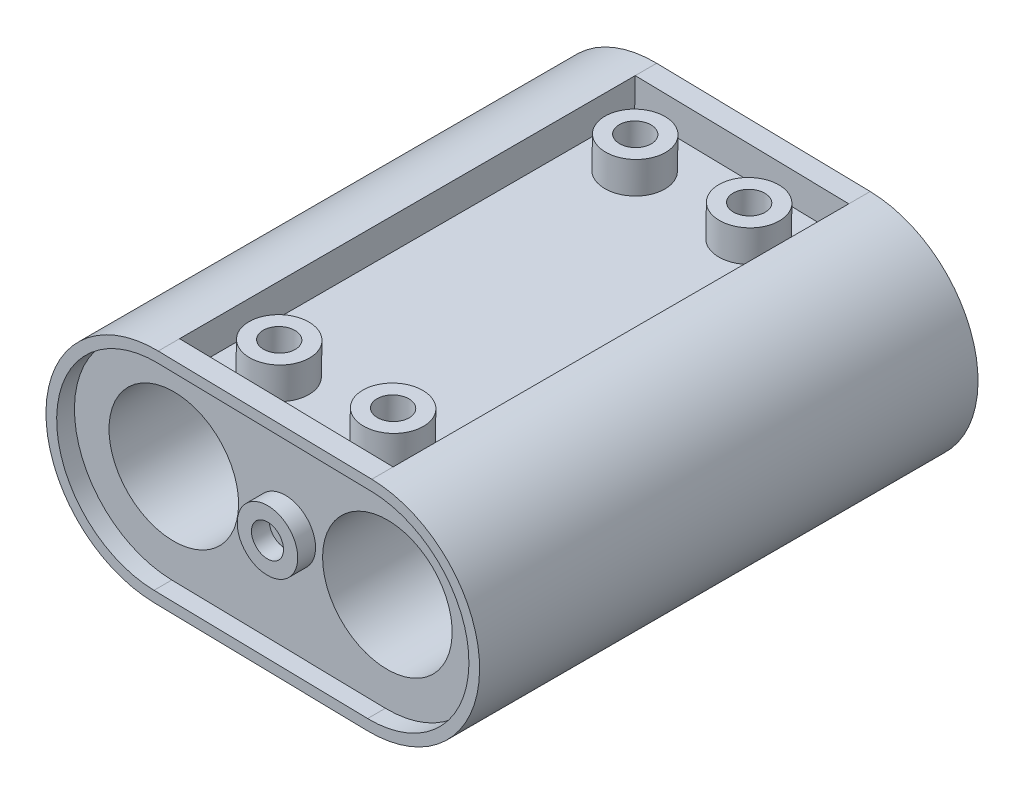
SolidWorks part; units mm, degrees
ref_plane "Спереди" through (0, 0, 0) normal (0, 0, 1) x (1, 0, 0)
ref_plane "Сверху" through (0, 0, 0) normal (0, 1, 0) x (1, 0, 0)
ref_plane "Справа" through (0, 0, 0) normal (1, 0, 0) x (0, 0, -1)
sketch "Эскиз1" plane through (0, 0, 0) normal (0, 0, 1) x (1, 0, 0)
  line L0 (0, 32.6386) -> (-1.3723, -35.9944) construction
  line L1 (-15.6574, -0.089) -> (14.3366, -0.6887) construction
  line L2 (-15.3485, 15.3597) -> (14.6455, 14.76)
  line L3 (-15.9662, -15.5377) -> (14.0278, -16.1374)
  circle A0 centre (-15.6574, -0.089) radius 9.1
  circle A1 centre (14.3366, -0.6887) radius 9.1
  arc A2 (-15.3485, 15.3597) -> (-15.9662, -15.5377) centre (-15.6574, -0.089) ccw
  arc A3 (14.0278, -16.1374) -> (14.6455, 14.76) centre (14.3366, -0.6887) ccw
  point P6 (-0.6604, -0.3889)
  dimension "D1" = 18.2
  dimension "D2" = 15
extrude "Бобышка-Вытянуть1" add sketch "Эскиз1" along normal blind 65
sketch "Эскиз2" plane through (0, 0, 65) normal (0, 0, 1) x (1, 0, 0)
  line L0 (-15.6574, -0.089) -> (14.3366, -0.6887) construction
  line L1 (-15.3785, 13.86) -> (14.6155, 13.2603)
  line L2 (-15.9363, -14.038) -> (14.0577, -14.6377)
  line L3 (14.6455, 14.76) -> (-15.3485, 15.3597) construction
  line L4 (-15.9662, -15.5377) -> (14.0278, -16.1374) construction
  line L5 (-15.9662, -15.5377) -> (14.0278, -16.1374)
  line L6 (14.6455, 14.76) -> (-15.3485, 15.3597)
  arc A0 (-15.3785, 13.86) -> (-15.9363, -14.038) centre (-15.6574, -0.089) ccw
  arc A1 (14.0577, -14.6377) -> (14.6155, 13.2603) centre (14.3366, -0.6887) ccw
  arc A2 (14.0278, -16.1374) -> (14.6455, 14.76) centre (14.3366, -0.6887) ccw construction
  arc A3 (-15.3485, 15.3597) -> (-15.9662, -15.5377) centre (-15.6574, -0.089) ccw construction
  arc A4 (14.0278, -16.1374) -> (14.6455, 14.76) centre (14.3366, -0.6887) ccw
  arc A5 (-15.3485, 15.3597) -> (-15.9662, -15.5377) centre (-15.6574, -0.089) ccw
  point P4 (-0.6604, -0.3889)
  dimension "D1" = 1.5
extrude "Бобышка-Вытянуть2" add sketch "Эскиз2" along normal blind 2.5
sketch "Эскиз3" plane through (0, 0, 65) normal (0, 0, 1) x (1, 0, 0)
  circle A0 centre (0, 0) radius 2.25
  circle A1 centre (0, 0) radius 4.25
  dimension "D1" = 4.5
  dimension "D2" = 2
sketch "Эскиз4" plane through (0, 0, 0) normal (0, 0, -1) x (-1, 0, 0)
  circle A0 centre (0, 0) radius 2.25
  circle A1 centre (0, 0) radius 4.1595
  dimension "D1" = 4.5
sketch "Эскиз5" plane through (0, 0, 0) normal (0, 0, -1) x (-1, 0, 0)
  line L0 (15.6574, -0.089) -> (-14.3366, -0.6887) construction
  line L1 (15.9662, -15.5377) -> (-14.0278, -16.1374)
  line L2 (15.3485, 15.3597) -> (-14.6455, 14.76)
  line L3 (-14.3366, -0.6887) -> (15.6574, -0.089) construction
  line L4 (-14.6155, 13.2603) -> (15.3785, 13.86)
  line L5 (-14.0577, -14.6377) -> (15.9363, -14.038)
  line L6 (-14.6455, 14.76) -> (15.3485, 15.3597) construction
  arc A0 (15.9662, -15.5377) -> (15.3485, 15.3597) centre (15.6574, -0.089) ccw
  arc A1 (-14.6455, 14.76) -> (-14.0278, -16.1374) centre (-14.3366, -0.6887) ccw
  arc A2 (-14.6155, 13.2603) -> (-14.0577, -14.6377) centre (-14.3366, -0.6887) ccw
  arc A3 (15.9363, -14.038) -> (15.3785, 13.86) centre (15.6574, -0.089) ccw
  point P4 (0.6604, -0.3889)
  point P9 (0.6604, -0.3889)
  dimension "D1" = 1.5
extrude "Бобышка-Вытянуть3" add sketch "Эскиз5" along normal blind 2.5
sketch "Эскиз7" plane through (0.3008, 15.0468, 0) normal (0.02, 0.9998, 0) x (0.9998, -0.02, 0)
  line L0 (14.3475, -67.5) -> (-15.6525, -67.5) construction
  line L1 (14.3475, -64.5) -> (-15.6525, -64.5)
  line L2 (14.3475, -64.5) -> (14.3475, -0.5)
  line L3 (14.3475, -0.5) -> (-15.6525, -0.5)
  line L4 (-15.6525, -64.5) -> (-15.6525, -0.5)
  line L5 (-15.6525, 2.5) -> (14.3475, 2.5) construction
  line L6 (-15.6525, -67.5) -> (-15.6525, 2.5) construction
  line L7 (14.3475, -67.5) -> (14.3475, 2.5) construction
  dimension "D1" = 3
  dimension "D2" = 3
extrude "Вырез-Вытянуть4" cut sketch "Эскиз7" against normal blind 4.5
sketch "Эскиз8" plane through (-0.3169, -15.8506, 0) normal (-0.02, -0.9998, 0) x (-0.9998, 0.02, 0)
  line L0 (15.6525, -67.5) -> (15.6525, 2.5) construction
  line L1 (15.6525, -0.5) -> (-14.3475, -0.5)
  line L2 (15.6525, -0.5) -> (15.6525, -64.5)
  line L3 (15.6525, -64.5) -> (-14.3475, -64.5)
  line L4 (-14.3475, -0.5) -> (-14.3475, -64.5)
  line L5 (-14.3475, -67.5) -> (-14.3475, 2.5) construction
  line L6 (-14.3475, 2.5) -> (15.6525, 2.5) construction
  line L7 (15.6525, -67.5) -> (-14.3475, -67.5) construction
  dimension "D1" = 3
  dimension "D2" = 3
extrude "Вырез-Вытянуть5" cut sketch "Эскиз8" against normal blind 4.5
extrude "Бобышка-Вытянуть4" add sketch "Эскиз4" along normal blind 2.5
sketch "Эскиз10" plane through (0, 0, 0) normal (0, 0, -1) x (-1, 0, 0)
  circle A0 centre (0, 0) radius 2.25 construction
  circle A1 centre (0, 0) radius 2.25
extrude "Вырез-Вытянуть6" cut sketch "Эскиз10" against normal blind 2.5
sketch "Эскиз11" plane through (0.2109, 10.5477, 0) normal (0.02, 0.9998, 0) x (0.9998, -0.02, 0)
  line L0 (-0.6525, -0.5) -> (-0.6525, -64.5) construction
  line L1 (14.3475, -0.5) -> (-15.6525, -0.5) construction
  line L2 (-15.6525, -64.5) -> (14.3475, -64.5) construction
  line L3 (14.3475, -32.5) -> (-15.6525, -32.5) construction
  line L4 (14.3475, -64.5) -> (14.3475, -0.5) construction
  line L5 (-15.6525, -0.5) -> (-15.6525, -64.5) construction
  circle A0 centre (7.3475, -7.5) radius 2.25
  circle A1 centre (7.3475, -7.5) radius 4.25
  circle A2 centre (-8.6525, -7.5) radius 4.25
  circle A3 centre (-8.6525, -7.5) radius 2.25
  circle A4 centre (7.3475, -57.5) radius 2.25
  circle A5 centre (7.3475, -57.5) radius 4.25
  circle A6 centre (-8.6525, -57.5) radius 4.25
  circle A7 centre (-8.6525, -57.5) radius 2.25
  dimension "D1" = 4.5
  dimension "D2" = 2
  dimension "D3" = 7
  dimension "D4" = 7
extrude "Бобышка-Вытянуть5" add sketch "Эскиз11" along normal blind 4.5
extrude "Бобышка-Вытянуть6" add sketch "Эскиз3" along normal blind 2.5
sketch "Эскиз16" plane through (0, 0, 0) normal (0, 0, -1) x (-1, 0, 0)
  line L0 (0, 15.5365) -> (0, -15.5948) construction
  line L1 (15.3785, 13.86) -> (-14.6155, 13.2603) construction
  line L2 (-8, 13.3925) -> (8, 13.7124)
  line L3 (-8, 13.3925) -> (-7.7154, 7.8925)
  line L4 (-7.7154, 7.8925) -> (8.2846, 8.2124)
  line L5 (8, 13.7124) -> (8.2846, 8.2124)
  point P6 (0, 13.5525)
  point P7 (-7.5, 11.7338)
  point P8 (7.5, 7.1986)
  point P9 (0, 0)
  point P10 (-7.5, 12.3986)
  point P12 (0, 0)
  point P13 (7.5, 12.3986)
  point P14 (0, 0)
  point P15 (0, 0)
  point P16 (0, 0)
  point P17 (0, 0)
  point P18 (0, 0)
  point P19 (0, 0)
  point P20 (6.957, 11.7395)
  point P21 (7.5947, 12.4073)
  point P22 (0, 0)
  point P25 (0, 0)
  point P26 (0, 0)
  point P27 (0, 0)
  point P28 (0, 0)
  point P29 (7.1674, 6.9304)
  point P30 (-6.4793, 7.0519)
  point P31 (-7.1674, 7.1493)
  point P32 (-7.1674, 7.2979)
  point P33 (7.357, 8.0848)
  point P34 (-6.8829, 7.4876)
  point P35 (0, 0)
  dimension "D1" = 5.5
  dimension "D2" = 16
